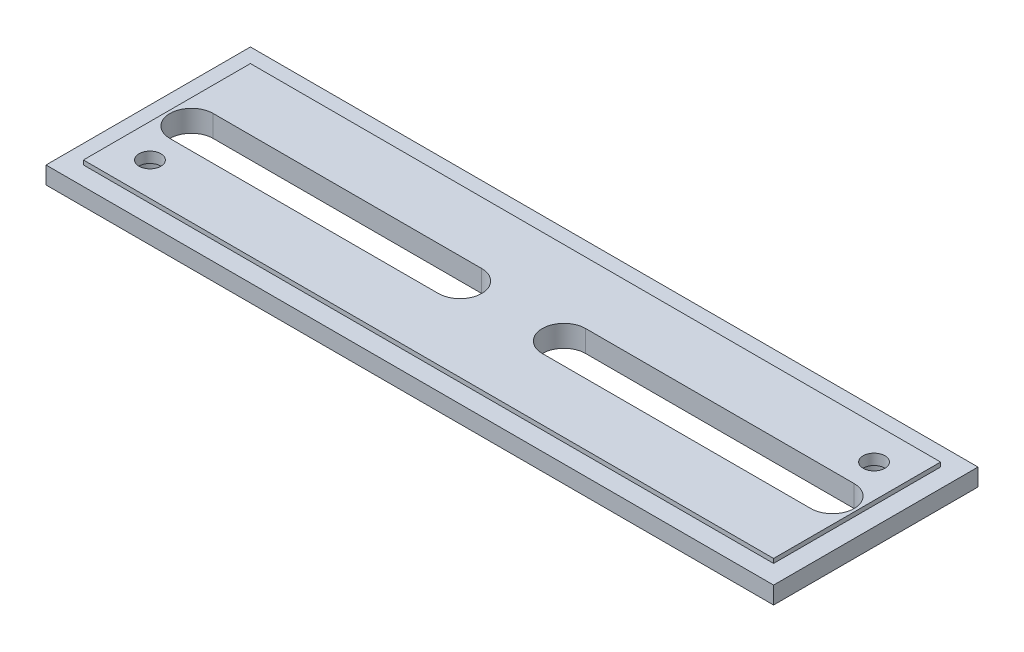
SolidWorks part; units mm, degrees
ref_plane "Front Plane" through (0, 0, 0) normal (0, 0, 1) x (1, 0, 0)
ref_plane "Top Plane" through (0, 0, 0) normal (0, 1, 0) x (1, 0, 0)
ref_plane "Right Plane" through (0, 0, 0) normal (1, 0, 0) x (0, 0, -1)
sketch "Sketch1" plane through (0, 0, 0) normal (0, 1, 0) x (1, 0, 0)
  line L1 (-66.675, -18.7325) -> (66.675, -18.7325)
  line L2 (-66.675, -18.7325) -> (-66.675, 18.7325)
  line L3 (-66.675, 18.7325) -> (66.675, 18.7325)
  line L4 (66.675, -18.7325) -> (66.675, 18.7325)
  line L5 (-66.675, -18.7325) -> (66.675, 18.7325) construction
  line L6 (-66.675, 18.7325) -> (66.675, -18.7325) construction
  point P0 (0, 0)
  dimension "D1" = 133.35
  dimension "D2" = 37.465
extrude "Boss-Extrude1" add sketch "Sketch1" along normal blind 3.175
sketch "Sketch2" plane through (0, 3.175, 0) normal (0, 1, 0) x (1, 0, 0)
  line L0 (63.246, 0) -> (66.675, 0) construction
  line L1 (-63.246, -15.3035) -> (63.246, -15.3035)
  line L2 (-63.246, -15.3035) -> (-63.246, 15.3035)
  line L3 (-63.246, 15.3035) -> (63.246, 15.3035)
  line L4 (63.246, -15.3035) -> (63.246, 15.3035)
  line L5 (-63.246, -15.3035) -> (63.246, 15.3035) construction
  line L6 (-63.246, 15.3035) -> (63.246, -15.3035) construction
  line L7 (66.675, -18.7325) -> (66.675, 18.7325) construction
  line L8 (0, 15.3035) -> (0, 18.7325) construction
  line L9 (66.675, 18.7325) -> (-66.675, 18.7325) construction
  point P0 (0, 0)
  dimension "D1" = 3.429
extrude "Boss-Extrude2" add sketch "Sketch2" along normal blind 0.7937
sketch "Sketch3" plane through (0, 0, 0) normal (0, 1, 0) x (1, 0, 0)
  line L0 (-9.525, 0) -> (-58.7375, 0) construction
  line L1 (-9.525, -3.9688) -> (-58.7375, -3.9688)
  line L2 (-9.525, 3.9688) -> (-58.7375, 3.9687)
  arc A0 (-9.525, -3.9688) -> (-9.525, 3.9688) centre (-9.525, 0) ccw
  arc A1 (-58.7375, 3.9687) -> (-58.7375, -3.9688) centre (-58.7375, 0) ccw
  point P3 (-34.1313, 0)
  dimension "D1" = 9.525
  dimension "D2" = 58.7375
  dimension "D3" = 7.9375
extrude "Cut-Extrude1" cut sketch "Sketch3" along normal up to next (3.9688 mm away)
mirror "Mirror1" about plane through (0, 0, 0) normal (1, 0, 0) of "Cut-Extrude1"
sketch "Sketch5" plane through (0, 0, 0) normal (0, 1, 0) x (1, 0, 0)
  line L0 (57.15, 9.2075) -> (-57.15, -9.2075) construction
  line L1 (-66.675, -18.7325) -> (66.675, -18.7325) construction
  line L2 (-66.675, 18.7325) -> (-66.675, -18.7325) construction
  circle A0 centre (-57.15, -9.2075) radius 2
  circle A1 centre (57.15, 9.2075) radius 2
  point P4 (0, 0)
  dimension "D1" = 4
  dimension "D2" = 9.525
  dimension "D3" = 9.525
extrude "Cut-Extrude2" cut sketch "Sketch5" along normal up to next
sketch "Sketch6" plane through (0, 0, 0) normal (0, -1, 0) x (-1, 0, 0)
  circle A0 centre (57.15, -9.2075) radius 3.175
  circle A1 centre (-57.15, 9.2075) radius 3.175
  dimension "D1" = 6.35
extrude "Cut-Extrude3" cut sketch "Sketch6" against normal blind 2
